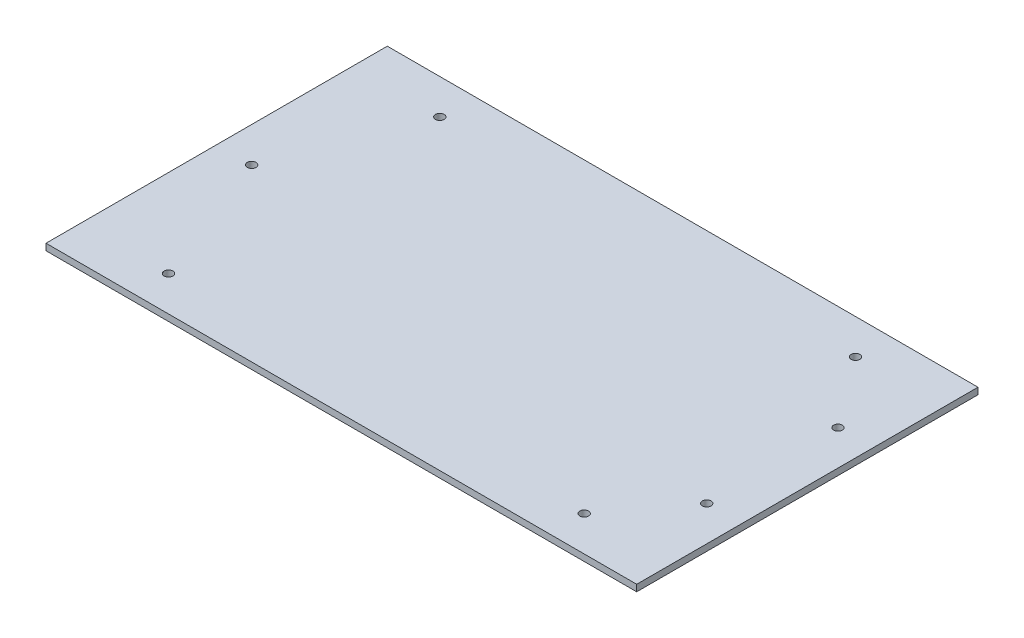
SolidWorks part; units mm, degrees
ref_plane "Front" through (0, 0, 0) normal (0, 0, 1) x (1, 0, 0)
ref_plane "Top" through (0, 0, 0) normal (0, 1, 0) x (1, 0, 0)
ref_plane "Right" through (0, 0, 0) normal (1, 0, 0) x (0, 0, -1)
sketch "Sketch1" plane through (0, 0, 0) normal (0, 1, 0) x (1, 0, 0)
  line L1 (135, 78) -> (-135, 78)
  line L2 (135, 78) -> (135, -78)
  line L3 (135, -78) -> (-135, -78)
  line L4 (-135, 78) -> (-135, -78)
  line L5 (135, 78) -> (-135, -78) construction
  line L6 (135, -78) -> (-135, 78) construction
  point P0 (0, 0)
  dimension "D1" = 156
  dimension "D2" = 270
extrude "Boss-Extrude1" add sketch "Sketch1" along normal blind 3 contours L1 L4 L3 L2
sketch "Sketch2" plane through (0, 3, 0) normal (0, 1, 0) x (1, 0, 0)
  line L0 (-135, 78) -> (-135, -78) construction
  circle A0 centre (-119, 0) radius 2
  point P5 (0, 0)
  dimension "D1" = 4
  dimension "D2" = 16
extrude "Cut-Extrude1" cut sketch "Sketch2" against normal up to next
sketch "Sketch3" plane through (0, 3, 0) normal (0, 1, 0) x (1, 0, 0)
  line L0 (135, 78) -> (-135, 78) construction
  line L2 (-135, 78) -> (-135, -78) construction
  circle A0 centre (-95, 62) radius 2
  dimension "D1" = 4
  dimension "D2" = 40
  dimension "D3" = 16
extrude "Cut-Extrude2" cut sketch "Sketch3" against normal up to next (3 mm away)
mirror "Mirror3" about plane through (0, 0, 0) normal (1, 0, 0) of "Cut-Extrude2"
mirror "Mirror4" about plane through (0, 0, 0) normal (0, 0, 1) of "Mirror3", "Cut-Extrude2"
sketch "Sketch5" plane through (0, 3, 0) normal (0, 1, 0) x (1, 0, 0)
  line L0 (135, 78) -> (135, -78) construction
  circle A0 centre (119, 30) radius 2
  circle A1 centre (119, -30) radius 2
  point P6 (0, 0)
  dimension "D1" = 4
  dimension "D2" = 16
  dimension "D3" = 30
  dimension "D4" = 30
extrude "Cut-Extrude4" cut sketch "Sketch5" against normal up to next
